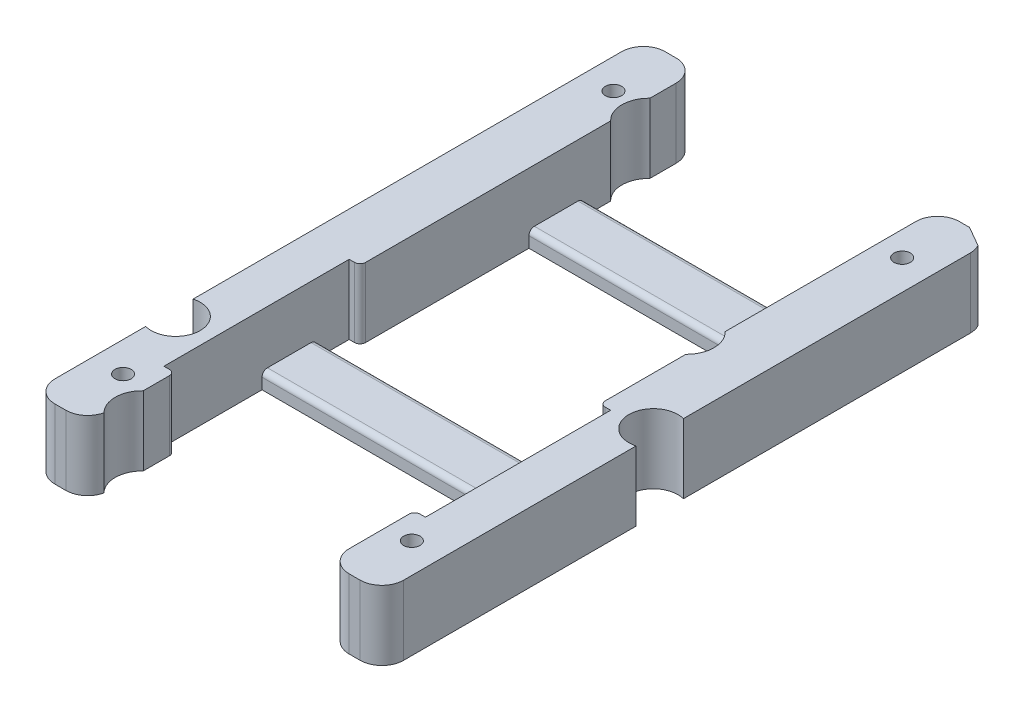
SolidWorks part; units mm, degrees
ref_plane "Front Plane" through (0, 0, 0) normal (0, 0, 1) x (1, 0, 0)
ref_plane "Top Plane" through (0, 0, 0) normal (0, 1, 0) x (1, 0, 0)
ref_plane "Right Plane" through (0, 0, 0) normal (1, 0, 0) x (0, 0, -1)
sketch "Sketch1" plane through (0, 0, 0) normal (0, 1, 0) x (1, 0, 0)
  line L0 (-22, 0) -> (-22, 112)
  line L2 (-22, 0) -> (-32, 0)
  line L3 (-32, 0) -> (-32, 112)
  line L5 (0, 0) -> (0, 112) construction
  line L6 (32, 0) -> (32, 112)
  line L7 (22, 0) -> (32, 0)
  line L8 (22, 0) -> (22, 112)
  line L9 (-32, 112) -> (-22, 112)
  line L10 (22, 112) -> (32, 112)
  dimension "D2" = 10
  dimension "D3" = 112
  dimension "D4" = 64
extrude "Boss-Extrude1" add sketch "Sketch1" along normal blind 12.75 contours L9 L3 L2 L0 | L8 L10 L6 L7
sketch "Sketch2" plane through (0, 12.75, 0) normal (0, 1, 0) x (1, 0, 0)
  line L0 (-32, 56) -> (32, 56) construction
  line L1 (-32, 112) -> (-22, 112) construction
  line L3 (0, 0) -> (0, 112) construction
  line L4 (-32, 0) -> (-32, 112) construction
  line L5 (32, 0) -> (32, 112) construction
  line L8 (22, 0) -> (32, 0) construction
  circle A0 centre (-26.5, 101) radius 1.5
  circle A1 centre (26.5, 101) radius 1.5
  circle A2 centre (26.5, 11) radius 1.5
  circle A3 centre (-26.5, 11) radius 1.5
  circle A4 centre (0, 38) radius 3
  dimension "D1" = 3
  dimension "D3" = 26.5
  dimension "D4" = 38
  dimension "D5" = 6
  dimension "D2" = 11
fillet "Fillet1" radius 4 4 edges at (32, 6.375, 0) (22, 6.375, 0) (32, 6.375, -112) (22, 6.375, -112)
fillet "Fillet2" radius 4 4 edges at (-22, 6.375, 0) (-32, 6.375, 0) (-32, 6.375, -112) (-22, 6.375, -112)
extrude "Cut-Extrude1" cut sketch "Sketch2" against normal through all
sketch "Sketch3" plane through (0, 12.75, 0) normal (0, 1, 0) x (1, 0, 0)
  line L0 (0, 0) -> (0, 112) construction
  line L5 (24, 16) -> (-24, 16)
  line L6 (24, 16) -> (24, 50)
  line L7 (24, 50) -> (-24, 50)
  line L8 (-24, 16) -> (-24, 50)
  circle A0 centre (26.5, 11) radius 1.5 construction
  point P0 (-43.1964, 63.4451)
  point P8 (0, 16)
  dimension "D3" = 34
  dimension "D1" = 5
  dimension "D2" = 48
extrude "Cut-Extrude2" cut sketch "Sketch3" against normal blind 12.75
ref_plane "Plane1" through (0, 0, -38) normal (0, 0, 1) x (1, 0, 0)
sketch "Sketch4" plane through (0, 0, 0) normal (0, -1, 0) x (1, 0, 0)
  line L0 (29.1624, -111.25) -> (31.774, -109.75) construction
  line L1 (29.1624, -111.25) -> (3.4821, -126) construction
  line L2 (26, -112) -> (28, -112) construction
  circle A0 centre (18.5389, -69.4) radius 5
  circle A1 centre (-18.5389, -99.6) radius 5
  circle A2 centre (-18.5389, -6.6) radius 5
  circle A3 centre (30.8389, -51) radius 4.5
  circle A4 centre (-30.8389, -25) radius 4.5
  arc A5 (31.774, -109.75) -> (27.8567, -112) centre (28.6903, -108.9163) cw
  spline S0 degree 3 poles (31.774, -109.75) (30.4682, -110.5) (29.1624, -111.25) (27.8567, -112) knots 0 0 0 0 1 1 1 1
  dimension "D1" = 9
  dimension "D2" = 9
extrude "Cut-Extrude3" cut sketch "Sketch4" against normal through all
sketch "Sketch5" plane through (-22, 0, 0) normal (1, 0, 0) x (0, 0, -1)
  line L0 (50, 0) -> (95.9916, 0) construction
  line L1 (90.9916, 0) -> (80.9916, 0)
  line L2 (90.9916, 0) -> (90.9916, 3)
  line L3 (90.9916, 3) -> (80.9916, 3)
  line L4 (80.9916, 0) -> (80.9916, 3)
  line L5 (95.9916, 0) -> (95.9916, 12.75) construction
  dimension "D1" = 3
  dimension "D2" = 10
  dimension "D3" = 5
extrude "Boss-Extrude2" add sketch "Sketch5" along normal up to next (44 mm away)
sketch "Sketch6" plane through (-24, 0, 0) normal (1, 0, 0) x (0, 0, -1)
  line L0 (50, 0) -> (16, 0) construction
  line L1 (44, 0) -> (34, 0)
  line L2 (44, 0) -> (44, 3)
  line L3 (44, 3) -> (34, 3)
  line L4 (34, 0) -> (34, 3)
  line L5 (50, 12.75) -> (50, 0) construction
  point P8 (50, 6.375)
  dimension "D1" = 3
  dimension "D2" = 10
  dimension "D3" = 6
extrude "Boss-Extrude3" add sketch "Sketch6" along normal up to next
fillet "Fillet3" radius 1 8 edges at (0, 3, -90.9916) (0, 3, -80.9916) (0, 3, -44) (0, 3, -34) (22, 6.375, -50) (22, 6.375, -16) (-22, 6.375, -50) (-22, 6.375, -16)
